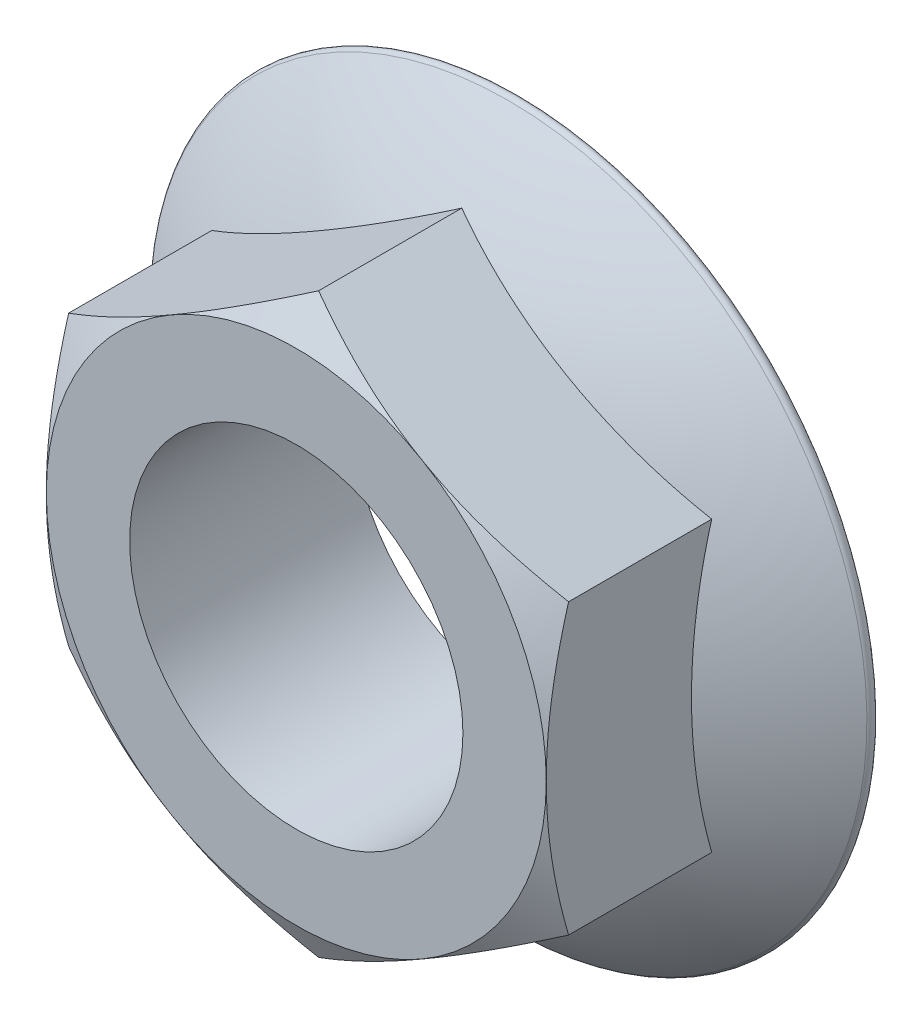
SolidWorks part; units mm, degrees
ref_plane "Front Plane" through (0, 0, 0) normal (0, 0, 1) x (1, 0, 0)
ref_plane "Top Plane" through (0, 0, 0) normal (0, 1, 0) x (1, 0, 0)
ref_plane "Right Plane" through (0, 0, 0) normal (1, 0, 0) x (0, 0, -1)
sketch "Sketch1" plane through (0, 0, 0) normal (0, 0, 1) x (1, 0, 0)
  line L1 (0, 25.9808) -> (-22.5, 12.9904)
  line L2 (-22.5, 12.9904) -> (-22.5, -12.9904)
  line L3 (-22.5, -12.9904) -> (0, -25.9808)
  line L4 (0, -25.9808) -> (22.5, -12.9904)
  line L5 (22.5, -12.9904) -> (22.5, 12.9904)
  line L6 (22.5, 12.9904) -> (0, 25.9808)
  circle A0 centre (0, 0) radius 22.5 construction
  dimension "D1" = 45
extrude "Boss-Extrude1" add sketch "Sketch1" along normal blind 20
sketch "Sketch2" plane through (0, 0, 0) normal (1, 0, 0) x (0, 0, -1)
  line L0 (0, 0) -> (-12, 0)
  line L2 (0, -31.95) -> (0, 0)
  line L3 (0, -12.9904) -> (0, 12.9904) construction
  arc A1 (-12, 0) -> (-0.894, -32.2578) centre (40.4001, 0) ccw
  arc A2 (-0.894, -32.2578) -> (0, -31.95) centre (-0.5, -31.95) ccw
  point P10 (0, -0.1146)
  dimension "D2" = 0.5
  dimension "D1" = 12
  dimension "D3" = 31.95
revolve "Revolve2" add sketch "Sketch2" angle 360 about L0
sketch "Sketch3" plane through (0, 0, 20) normal (0, 0, 1) x (1, 0, 0)
  circle A0 centre (0, 0) radius 22.5
extrude "Cut-Extrude1" cut sketch "Sketch3" against normal blind 20 draft 60 flip side to cut
sketch "Sketch4" plane through (0, 0, 20) normal (0, 0, 1) x (1, 0, 0)
  circle A0 centre (0, 0) radius 15
  dimension "D1" = 30
extrude "Cut-Extrude2" cut sketch "Sketch4" against normal up to next
cosmetic thread "Cosmetic Thread1" parameters "D2"=31.75
